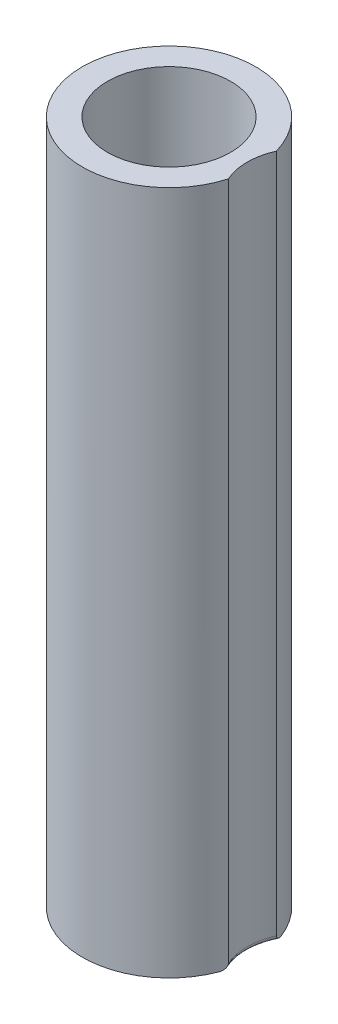
SolidWorks part; units mm, degrees
material "Cardboard"
ref_plane "Frontal Plane" through (0, 0, 0) normal (0, 0, 1) x (1, 0, 0)
ref_plane "Horizontal Plane" through (0, 0, 0) normal (0, 1, 0) x (1, 0, 0)
ref_plane "Profile Plane" through (0, 0, 0) normal (1, 0, 0) x (0, 0, -1)
sketch "Sketch1" plane through (0, 0, 0) normal (0, 1, 0) x (1, 0, 0)
  line L0 (0, 0) -> (11.9688, 0) construction
  circle A0 centre (0, 0) radius 6.3
  arc A1 (8.5273, 2.4597) -> (8.5273, -2.4597) centre (0, 0) ccw
  circle A2 centre (14, 0) radius 5.5 construction
  circle A3 centre (14, 0) radius 5.9 construction
  arc A4 (8.5273, 2.4597) -> (8.5273, -2.4597) centre (14, 0) ccw
  circle A5 centre (0, 0) radius 2 construction
  dimension "D1" = 12.6
  dimension "D2" = 17.75
  dimension "D3" = 6
  dimension "D4" = 14
  dimension "D5" = 11
  dimension "D6" = 11.8
extrude "Boss-Extrude1" add sketch "Sketch1" along normal blind 70
fillet "Fillet1" radius 0.5 1 edges at (8, 0, 0)
